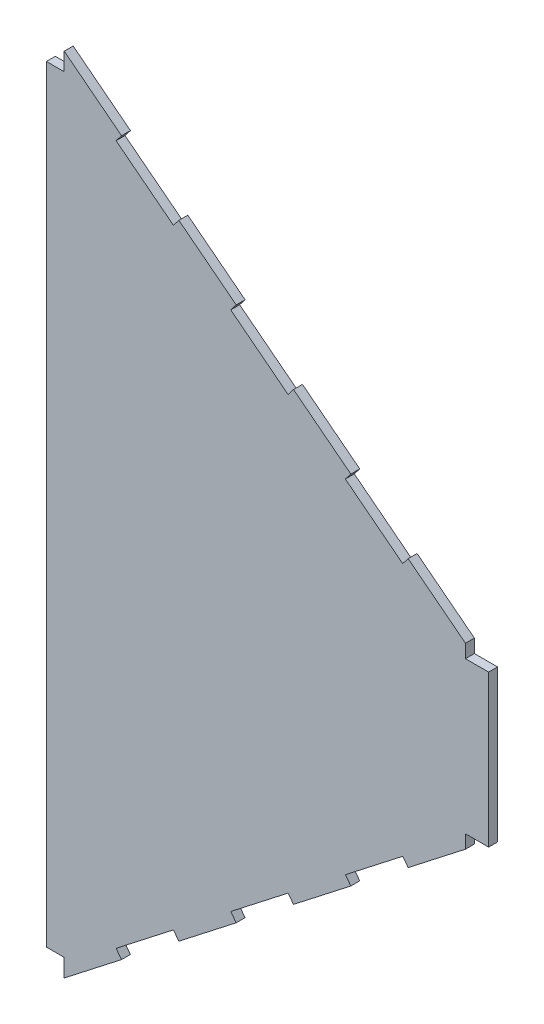
SolidWorks part; units mm, degrees
material "Contreplaqué pin"
ref_plane "Plan de face" through (0, 0, 0) normal (0, 0, 1) x (1, 0, 0)
ref_plane "Plan de dessus" through (0, 0, 0) normal (0, 1, 0) x (1, 0, 0)
ref_plane "Plan de droite" through (0, 0, 0) normal (1, 0, 0) x (0, 0, -1)
sketch "Esquisse1" plane through (0, 0, 0) normal (0, 0, 1) x (1, 0, 0)
  line L0 (0, 0) -> (0, 10)
  line L1 (0, 450) -> (32.1349, 425)
  line L2 (224.9444, 275) -> (224.9444, 267.5)
  line L3 (224.9444, 175) -> (192.8095, 150)
  line L4 (224.9444, 225) -> (-10, 225) construction
  line L5 (32.1349, 425) -> (29.0647, 421.0536)
  line L6 (29.0647, 421.0536) -> (61.1997, 396.0536)
  line L7 (61.1997, 396.0536) -> (64.2698, 400)
  line L8 (96.4048, 375) -> (93.3346, 371.0536)
  line L9 (93.3346, 371.0536) -> (125.4695, 346.0536)
  line L10 (125.4695, 346.0536) -> (128.5397, 350)
  line L11 (160.6746, 325) -> (157.6044, 321.0536)
  line L12 (157.6044, 321.0536) -> (189.7393, 296.0536)
  line L13 (189.7393, 296.0536) -> (192.8095, 300)
  line L14 (64.2698, 400) -> (96.4048, 375)
  line L15 (128.5397, 350) -> (160.6746, 325)
  line L16 (192.8095, 300) -> (224.9444, 275)
  line L17 (192.8095, 150) -> (224.9444, 175)
  line L18 (128.5397, 100) -> (160.6746, 125)
  line L19 (64.2698, 50) -> (96.4048, 75)
  line L20 (189.7393, 153.9464) -> (192.8095, 150)
  line L21 (157.6044, 128.9464) -> (189.7393, 153.9464)
  line L22 (160.6746, 125) -> (157.6044, 128.9464)
  line L23 (125.4695, 103.9464) -> (128.5397, 100)
  line L24 (93.3346, 78.9464) -> (125.4695, 103.9464)
  line L25 (96.4048, 75) -> (93.3346, 78.9464)
  line L26 (61.1997, 53.9464) -> (64.2698, 50)
  line L27 (29.0647, 28.9464) -> (61.1997, 53.9464)
  line L28 (32.1349, 25) -> (29.0647, 28.9464)
  line L29 (0, 0) -> (32.1349, 25)
  line L30 (32.1349, 25) -> (0, 0)
  line L31 (96.4048, 75) -> (64.2698, 50)
  line L32 (160.6746, 125) -> (128.5397, 100)
  line L33 (0, 440) -> (0, 450)
  line L34 (0, 440) -> (-10, 440)
  line L36 (0, 10) -> (-10, 10)
  line L37 (-10, 440) -> (-10, 10)
  line L38 (224.9444, 182.5) -> (224.9444, 175)
  line L39 (224.9444, 267.5) -> (237.9444, 267.5)
  line L41 (224.9444, 182.5) -> (237.9444, 182.5)
  line L42 (237.9444, 267.5) -> (237.9444, 182.5)
  dimension "D1" = 450
  dimension "D3" = 100
  dimension "D4" = 5
  dimension "D5" = 285
  dimension "D6" = 40.7143
  dimension "D7" = 40.7143
  dimension "D2" = 10
  dimension "D8" = 430
  dimension "D9" = 85
  dimension "D10" = 13
extrude "Boss.-Extru.1" add sketch "Esquisse1" along normal blind 5 contours L4 L2 L16 L13 L12 L11 L15 L10 L9 L8 L14 L7 L6 L5 L1 L0 | L2 L4 L0 L29 L28 L27 L26 L19 L25 L24 L23 L18 L22 L21 L20 L3
equation "\"D6@Esquisse1\"=\"D5@Esquisse1\"/7"
